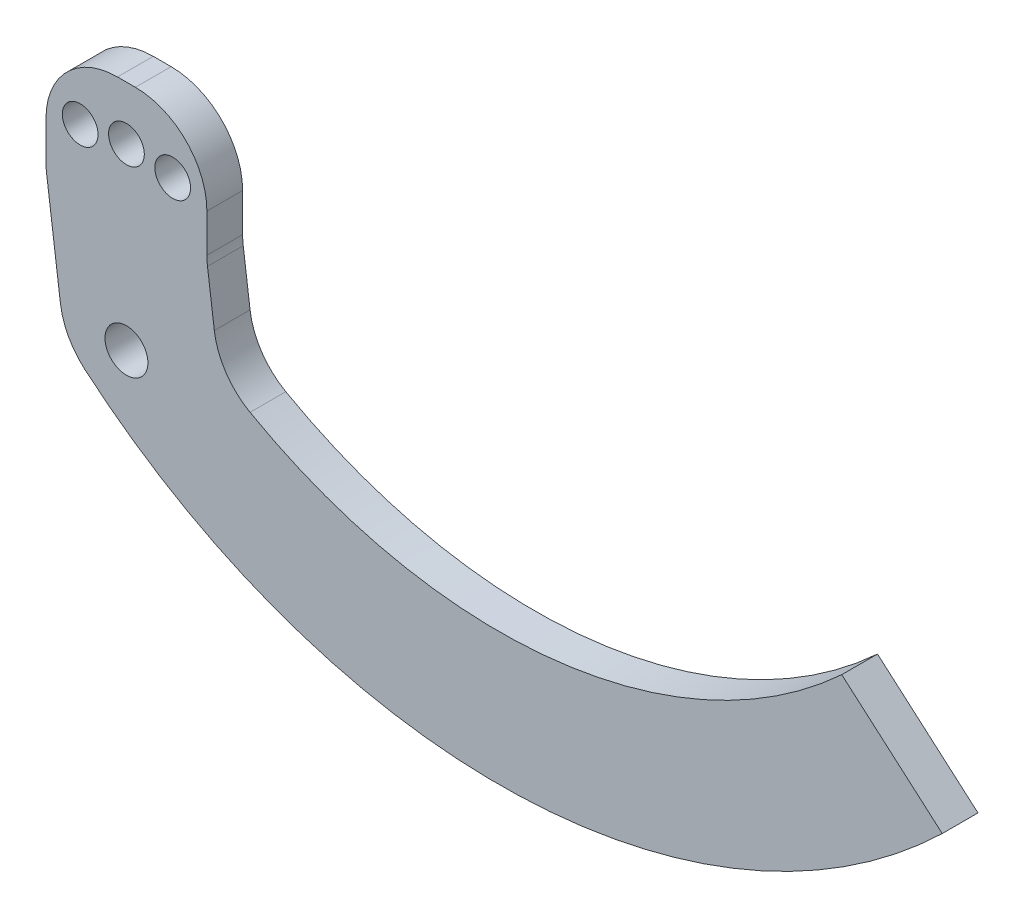
SolidWorks part; units mm, degrees
material "Acier non allié"
ref_plane "Plan de face" through (0, 0, 0) normal (0, 0, 1) x (1, 0, 0)
ref_plane "Plan de dessus" through (0, 0, 0) normal (0, 1, 0) x (1, 0, 0)
ref_plane "Plan de droite" through (0, 0, 0) normal (1, 0, 0) x (0, 0, -1)
sketch "Esquisse1" plane through (0, 0, 0) normal (0, 0, 1) x (1, 0, 0)
  line L0 (200.0832, -26.0007) -> (228.1933, -50.4365) construction
  line L1 (200.0832, -26.0007) -> (228.1933, -50.4365)
  line L2 (-22.5, -14.5) -> (-22.5, 17.5) construction
  line L3 (22.5, 17.5) -> (-22.5, 17.5) construction
  line L4 (22.5, -14.5) -> (22.5, 17.5) construction
  line L5 (-22.5, -14.5) -> (-22.5, 17.5)
  line L6 (22.5, 17.5) -> (-22.5, 17.5)
  line L7 (22.5, -14.5) -> (22.5, 17.5)
  line L8 (22.5, -14.5) -> (25.8147, -39.8259)
  line L9 (-22.5, -14.5) -> (-17.5, -52.7023)
  line L10 (-17.5, -52.7023) -> (25.8147, -39.8259) construction
  line L11 (-17.5, -97.5) -> (-17.5, -20.5) construction
  circle A0 centre (0, -47.5) radius 6 construction
  circle A1 centre (-12.941, 0.7963) radius 5 construction
  circle A2 centre (0, 2.5) radius 5 construction
  circle A3 centre (12.941, 0.7963) radius 5 construction
  circle A4 centre (0, -47.5) radius 6
  circle A5 centre (-12.941, 0.7963) radius 5
  circle A6 centre (0, 2.5) radius 5
  circle A7 centre (12.941, 0.7963) radius 5
  arc A8 (200.0832, -26.0007) -> (25.8147, -39.8259) centre (104.1519, 77.9745) cw
  arc A9 (228.1933, -50.4365) -> (-17.5, -52.7023) centre (104.1519, 77.9745) cw
extrude "Boss.-Extru.1" add sketch "Esquisse1" along normal mid plane 10
fillet "Congé1" radius 20 6 edges at (22.5, -14.5, 0) (22.5, 17.5, 0) (-22.5, 17.5, 0) (-17.5, -52.7023, 0) (-22.5, -14.5, 0) (25.8147, -39.8259, 0)
